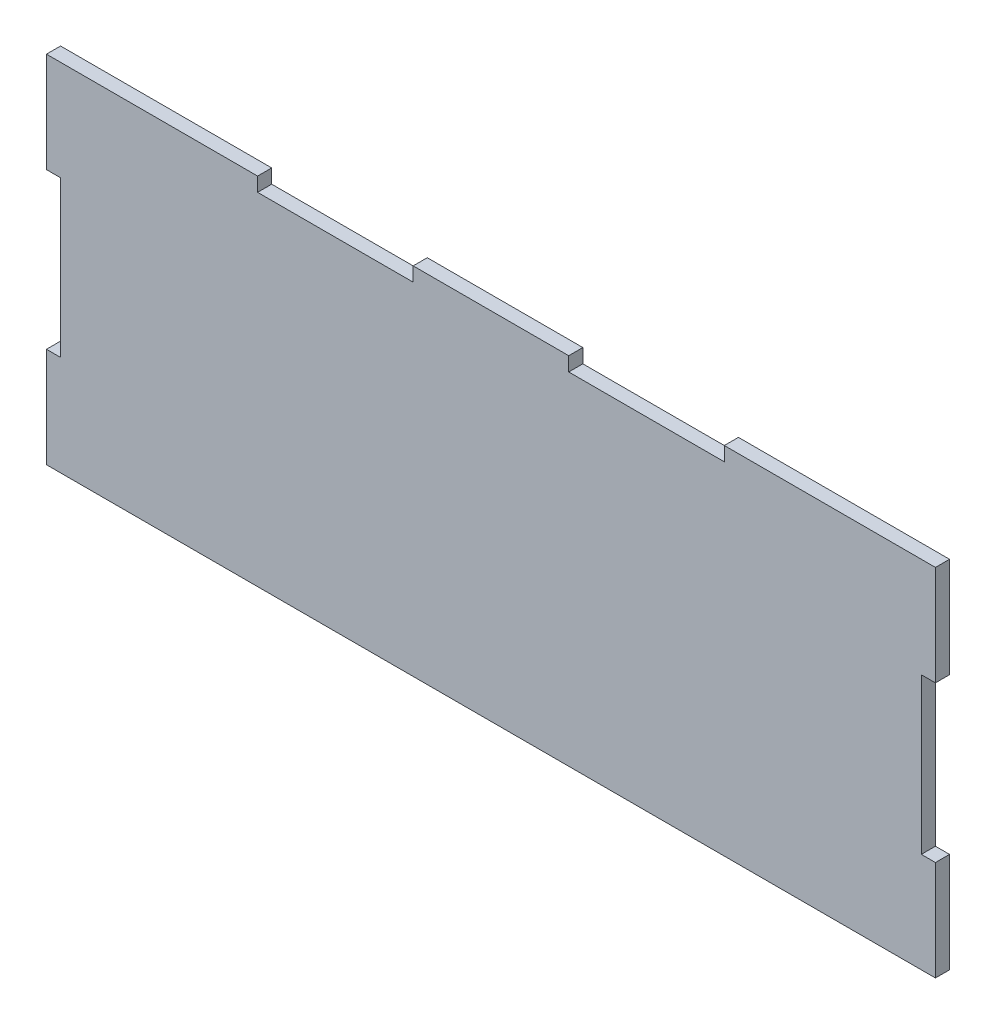
SolidWorks part; units mm, degrees
ref_plane "Plan de face" through (0, 0, 0) normal (0, 0, 1) x (1, 0, 0)
ref_plane "Plan de dessus" through (0, 0, 0) normal (0, 1, 0) x (1, 0, 0)
ref_plane "Plan de droite" through (0, 0, 0) normal (1, 0, 0) x (0, 0, -1)
sketch "Esquisse2" plane through (0, 0, 0) normal (0, 0, 1) x (1, 0, 0)
  line L1 (-100, 40) -> (100, 40)
  line L2 (-100, 40) -> (-100, -40)
  line L3 (-100, -40) -> (100, -40)
  line L4 (100, 40) -> (100, -40)
  point P4 (0, 40)
  point P6 (100, 0)
  dimension "D1" = 200
  dimension "D2" = 80
extrude "Boss.-Extru.1" add sketch "Esquisse2" along normal blind 3.175
sketch "Esquisse3" plane through (0, 0, 3.175) normal (0, 0, 1) x (1, 0, 0)
  line L0 (100, 40) -> (-100, 40) construction
  line L1 (17.5, 40) -> (52.5, 40)
  line L2 (17.5, 40) -> (17.5, 36.825)
  line L3 (17.5, 36.825) -> (52.5, 36.825)
  line L4 (52.5, 40) -> (52.5, 36.825)
  line L6 (-17.5, 40) -> (-52.5, 40)
  line L7 (-17.5, 40) -> (-17.5, 36.825)
  line L8 (-17.5, 36.825) -> (-52.5, 36.825)
  line L9 (-52.5, 40) -> (-52.5, 36.825)
  dimension "D1" = 3.175
  dimension "D2" = 3.175
  dimension "D3" = 35
  dimension "D4" = 35
  dimension "D5" = 35
  dimension "D6" = 17.5
extrude "Enlèv. mat.-Extru.1" cut sketch "Esquisse3" against normal through all
sketch "Esquisse4" plane through (0, 0, 3.175) normal (0, 0, 1) x (1, 0, 0)
  line L0 (-100, 40) -> (-100, -40) construction
  line L1 (-100, 17.5) -> (-96.825, 17.5)
  line L2 (-100, 17.5) -> (-100, -17.5)
  line L3 (-100, -17.5) -> (-96.825, -17.5)
  line L4 (-96.825, 17.5) -> (-96.825, -17.5)
  point P6 (-96.825, 0)
  dimension "D1" = 3.175
  dimension "D2" = 35
extrude "Enlèv. mat.-Extru.2" cut sketch "Esquisse4" against normal through all
mirror "Symétrie1" about plane through (0, 0, 0) normal (1, 0, 0) of "Enlèv. mat.-Extru.2"
